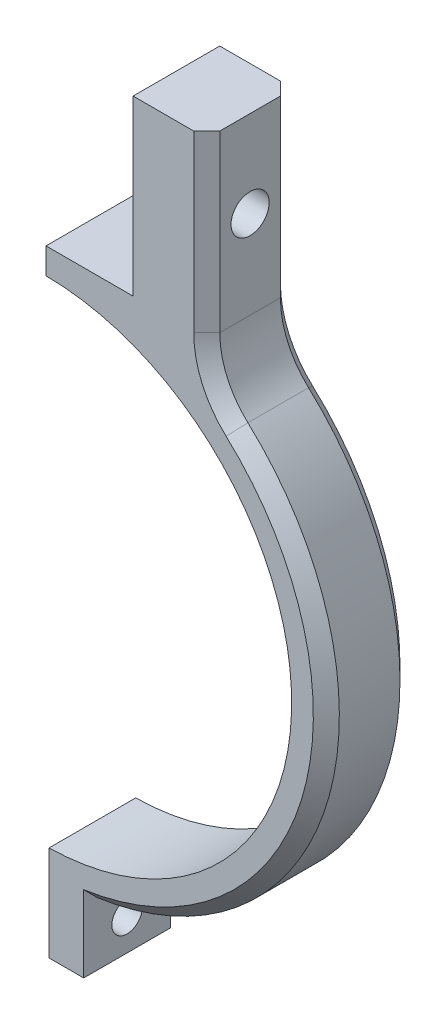
SolidWorks part; units mm, degrees
ref_plane "Ebene vorne" through (0, 0, 0) normal (0, 0, 1) x (1, 0, 0)
ref_plane "Ebene oben" through (0, 0, 0) normal (0, 1, 0) x (1, 0, 0)
ref_plane "Ebene rechts" through (0, 0, 0) normal (1, 0, 0) x (0, 0, -1)
sketch "Skizze1" plane through (0, 0, 0) normal (0, 0, 1) x (1, 0, 0)
  line L0 (0, 0) -> (0, 53.7291) construction
  line L14 (0, 0) -> (0, -44.1347) construction
  line L15 (0.5, -28.4956) -> (0.5, -32.4962)
  line L16 (-0.5, -28.4956) -> (-0.5, -32.4962)
  line L17 (0.5, -32.4962) -> (0.5, -39.4962)
  line L18 (0.5, -39.4962) -> (4.5, -39.4962)
  line L19 (4.5, -39.4962) -> (4.5, -32.187)
  line L20 (-4.5, -39.4962) -> (-4.5, -32.187)
  line L21 (-0.5, -39.4962) -> (-4.5, -39.4962)
  line L22 (-0.5, -32.4962) -> (-0.5, -39.4962)
  line L23 (-10.2, 31.5) -> (-10.2, 51.5)
  line L24 (-10.2, 51.5) -> (-18.7, 51.5)
  line L25 (-18.7, 51.5) -> (-18.7, 26.5812)
  line L26 (-10.2, 31.5) -> (10.2, 31.5)
  line L27 (0, 28.5) -> (12.0002, 28.5) construction
  line L28 (18.7, 51.5) -> (18.7, 26.5812)
  line L29 (10.2, 51.5) -> (18.7, 51.5)
  line L30 (10.2, 31.5) -> (10.2, 51.5)
  arc A0 (0.5, -28.4956) -> (-0.5, -28.4956) centre (0, 0) ccw
  arc A1 (-18.7, 26.5812) -> (-4.5, -32.187) centre (0, 0) ccw
  arc A2 (4.5, -32.187) -> (18.7, 26.5812) centre (0, 0) ccw
  point P10 (0, 33.5025)
  point P11 (0, 31.6594)
  point P17 (0, 31.5)
  point P18 (0, 39.6025)
  dimension "D1" = 57
  dimension "D2" = 4
  dimension "D3" = 20.4
  dimension "D4" = 20
  dimension "D5" = 3
  dimension "D6" = 8.5
  dimension "D10" = 1
  dimension "D11" = 4
  dimension "D12" = 7
extrude "Aufsatz-Linear austragen1" add sketch "Skizze1" along normal blind 10
sketch "Skizze2" plane through (-4.5, 0, 0) normal (-1, 0, 0) x (0, 0, 1)
  line L0 (0, -35.8416) -> (10, -35.8416) construction
  line L1 (0, -32.187) -> (0, -39.4962) construction
  line L2 (10, -32.187) -> (10, -39.4962) construction
  circle A0 centre (5, -35.8416) radius 1.75
  dimension "D1" = 3.5
extrude "Schnitt-Linear austragen1" cut sketch "Skizze2" against normal through all
sketch "Skizze3" plane through (0, 0, 10) normal (0, 0, 1) x (1, 0, 0)
  line L0 (-10.8174, 36.4205) -> (0, 26.8755)
  line L1 (0, 26.8755) -> (11.8484, 37.1414)
  line L2 (11.8484, 37.1414) -> (47.3746, 17.8863)
  line L3 (47.3746, 17.8863) -> (51.4546, -59.0738)
  line L4 (51.4546, -59.0738) -> (-81.1349, -43.2704)
  line L5 (-81.1349, -43.2704) -> (-40.9452, 68.8874)
  line L6 (-40.9452, 68.8874) -> (-10.8174, 36.4205)
extrude "Schnitt-Linear austragen2" [suppressed] cut sketch "Skizze3" against normal through all
sketch "Skizze4" plane through (-18.7, 0, 0) normal (-1, 0, 0) x (0, 0, 1)
  line L0 (5, 51.5) -> (5, 31.5) construction
  line L1 (10, 51.5) -> (0, 51.5) construction
  line L3 (10, 31.5) -> (0, 31.5) construction
  circle A0 centre (5, 41.5) radius 2.2
  dimension "D1" = 4.4
extrude "Schnitt-Linear austragen3" cut sketch "Skizze4" against normal through all
fillet "Verrundung1" radius 10 2 edges at (18.7, 26.5812, 5) (-18.7, 26.5812, 5)
sketch "Skizze5" plane through (-4.5, 0, 0) normal (-1, 0, 0) x (0, 0, 1)
  line L1 (2.25, -38.5916) -> (7.75, -38.5916)
  line L2 (2.25, -38.5916) -> (2.25, -33.0916)
  line L3 (2.25, -33.0916) -> (7.75, -33.0916)
  line L4 (7.75, -38.5916) -> (7.75, -33.0916)
  line L5 (2.25, -38.5916) -> (7.75, -33.0916) construction
  line L6 (2.25, -33.0916) -> (7.75, -38.5916) construction
  point P0 (5, -35.8416)
  dimension "D1" = 5.5
extrude "Schnitt-Linear austragen4" cut sketch "Skizze5" against normal blind 2
chamfer "Fase1" distance 1.5 angle 45 12 edges at (-18.7, 41.4229, 0) (-18.7, 41.4229, 10) (-19.5477, 27.3165, 10) (-19.5477, 27.3165, 0) (-31.0366, -9.6425, 10) (-31.0366, -9.6425, 0) (18.7, 41.4229, 10) (18.7, 41.4229, 0) (19.5477, 27.3165, 10) (19.5477, 27.3165, 0) (31.0366, -9.6425, 0) (31.0366, -9.6425, 10)
sketch "Skizze6" plane through (0, 0, 0) normal (0, 0, 1) x (1, 0, 0)
  line L0 (0, -82.9146) -> (0, 27.8305)
  line L1 (0, 82.9146) -> (-62.1698, 71.0203)
  line L2 (-62.1698, 71.0203) -> (-62.1698, -54.9185)
  line L3 (-62.1698, -54.9185) -> (0, -82.9146)
  line L4 (0, 32.2084) -> (0.15, 32.2084)
  line L5 (0.15, 32.2084) -> (0.15, 27.8305)
  line L6 (0.15, 27.8305) -> (0, 27.8305)
  line L7 (0, 32.2084) -> (0, 82.9146)
  point P4 (0, 0)
  dimension "D1" = 0.15
extrude "Schnitt-Linear austragen5" cut sketch "Skizze6" along normal through all
